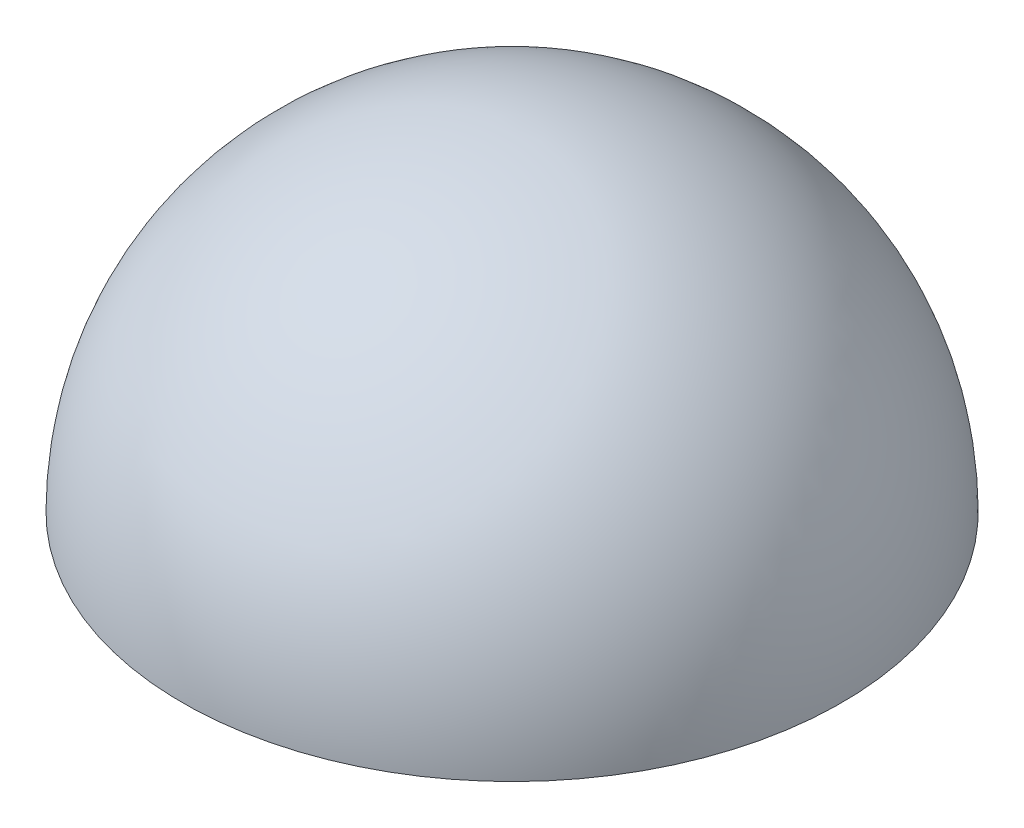
SolidWorks part; units mm, degrees
ref_plane "Front Plane" through (0, 0, 0) normal (0, 0, 1) x (1, 0, 0)
ref_plane "Top Plane" through (0, 0, 0) normal (0, 1, 0) x (1, 0, 0)
ref_plane "Right Plane" through (0, 0, 0) normal (1, 0, 0) x (0, 0, -1)
sketch "Sketch1" plane through (0, 0, 0) normal (0, 1, 0) x (1, 0, 0)
  line L0 (0, 0) -> (0, 4597.4) construction
  line L1 (0, 0) -> (0, -4597.4) construction
  circle A0 centre (0, 0) radius 4597.4 construction
sketch "Sketch2" plane through (0, 0, 0) normal (0, 1, 0) x (1, 0, 0)
  line L0 (0, 4597.4) -> (0, -4597.4) construction
  line L1 (0, 4597.4) -> (0, 4622.8)
  line L2 (0, -4597.4) -> (0, -4622.8)
  line L3 (0, 0) -> (4597.4, 0) construction
  line L4 (4597.4, 0) -> (4622.8, 0) construction
  arc A0 (0, 4597.4) -> (0, -4597.4) centre (0, 0) cw
  arc A1 (0, 4622.8) -> (0, -4622.8) centre (0, 0) cw
revolve "Revolve1" add sketch "Sketch2" angle 180 about L0
